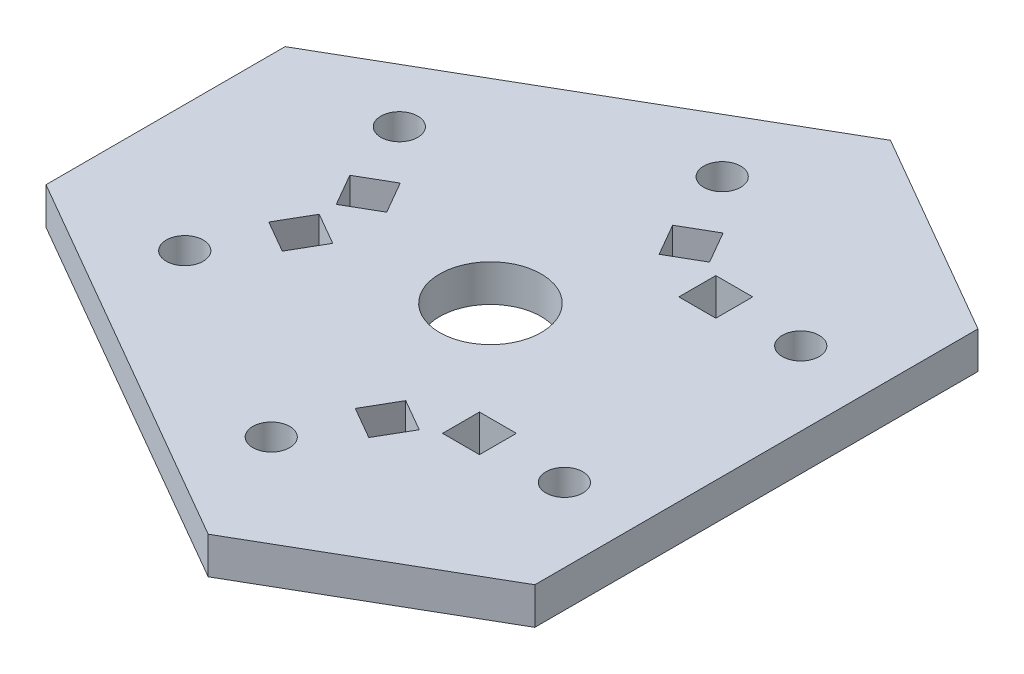
SolidWorks part; units mm, degrees
ref_plane "Front Plane" through (0, 0, 0) normal (0, 0, 1) x (1, 0, 0)
ref_plane "Top Plane" through (0, 0, 0) normal (0, 1, 0) x (1, 0, 0)
ref_plane "Right Plane" through (0, 0, 0) normal (1, 0, 0) x (0, 0, -1)
sketch "Sketch2" plane through (0, 0, 0) normal (0, 1, 0) x (1, 0, 0)
  line L0 (0, 0) -> (-43656.8426, 0) construction
  line L1 (22.8681, 19.05) -> (22.8681, -19.05)
  line L2 (22.8681, 39.6088) -> (-45.7363, 0) construction
  line L3 (-45.7363, 0) -> (22.8681, -39.6088) construction
  line L4 (22.8681, -39.6088) -> (22.8681, 39.6088) construction
  line L5 (22.8681, -19.05) -> (5.0637, -29.3294)
  line L6 (5.0637, -29.3294) -> (-27.9319, -10.2794)
  line L7 (-0.0355, 0.0615) -> (21828.3858, -37807.8732) construction
  line L8 (40.0162, 69.3101) -> (-21788.4051, -37738.6247) construction
  line L9 (-27.9319, -10.2794) -> (-27.9319, 10.2794)
  line L10 (-27.9319, 10.2794) -> (5.0637, 29.3294)
  line L11 (5.0637, 29.3294) -> (22.8681, 19.05)
  line L12 (7.6281, 8.5725) -> (10.8031, 8.5725)
  line L13 (7.6281, -8.5725) -> (10.8031, -8.5725)
  line L14 (7.6281, -8.5725) -> (7.6281, -11.7475)
  line L15 (7.6281, -11.7475) -> (10.8031, -11.7475)
  line L16 (10.8031, -8.5725) -> (10.8031, -11.7475)
  line L17 (10.8031, 8.5725) -> (10.8031, 11.7475)
  line L18 (7.6281, 11.7475) -> (10.8031, 11.7475)
  line L19 (7.6281, 8.5725) -> (7.6281, 11.7475)
  line L20 (3.6099, -10.8924) -> (2.0224, -13.642)
  line L21 (2.0224, -13.642) -> (4.7721, -15.2295)
  line L22 (6.3596, -12.4799) -> (4.7721, -15.2295)
  line L23 (3.6099, -10.8924) -> (6.3596, -12.4799)
  line L24 (-11.2381, -2.3199) -> (-12.8256, -5.0695)
  line L25 (-11.2381, -2.3199) -> (-13.9877, -0.7324)
  line L26 (-13.9877, -0.7324) -> (-15.5752, -3.482)
  line L27 (-12.8256, -5.0695) -> (-15.5752, -3.482)
  line L28 (-11.2381, 2.3199) -> (-12.8256, 5.0695)
  line L29 (-12.8256, 5.0695) -> (-15.5752, 3.482)
  line L30 (-13.9877, 0.7324) -> (-15.5752, 3.482)
  line L31 (-11.2381, 2.3199) -> (-13.9877, 0.7324)
  line L32 (3.6099, 10.8924) -> (2.0224, 13.642)
  line L33 (3.6099, 10.8924) -> (6.3596, 12.4799)
  line L34 (6.3596, 12.4799) -> (4.7721, 15.2295)
  line L35 (2.0224, 13.642) -> (4.7721, 15.2295)
  circle A0 centre (0, 0) radius 45.7363 construction
  circle A1 centre (16.5181, 10.16) radius 1.5875
  circle A2 centre (16.5181, -10.16) radius 1.5875
  circle A3 centre (0.5397, -19.3851) radius 1.5875
  circle A4 centre (0, 0) radius 4.3656
  circle A5 centre (-17.0579, -9.2251) radius 1.5875
  circle A6 centre (-17.0579, 9.2251) radius 1.5875
  circle A7 centre (0.5397, 19.3851) radius 1.5875
  point P34 (7.6281, -10.16)
  dimension "D2" = 3.175
  dimension "D3" = 8.7312
  dimension "D1" = 38.1
  dimension "D4" = 20.32
  dimension "D5" = 6.35
  dimension "D6" = 50.8
  dimension "D8" = 15.24
  dimension "D9" = 3.175
  dimension "D10" = 3.175
  dimension "D7" = 3
  dimension "D11" = 3
extrude "Boss-Extrude2" add sketch "Sketch2" along normal blind 3.175
